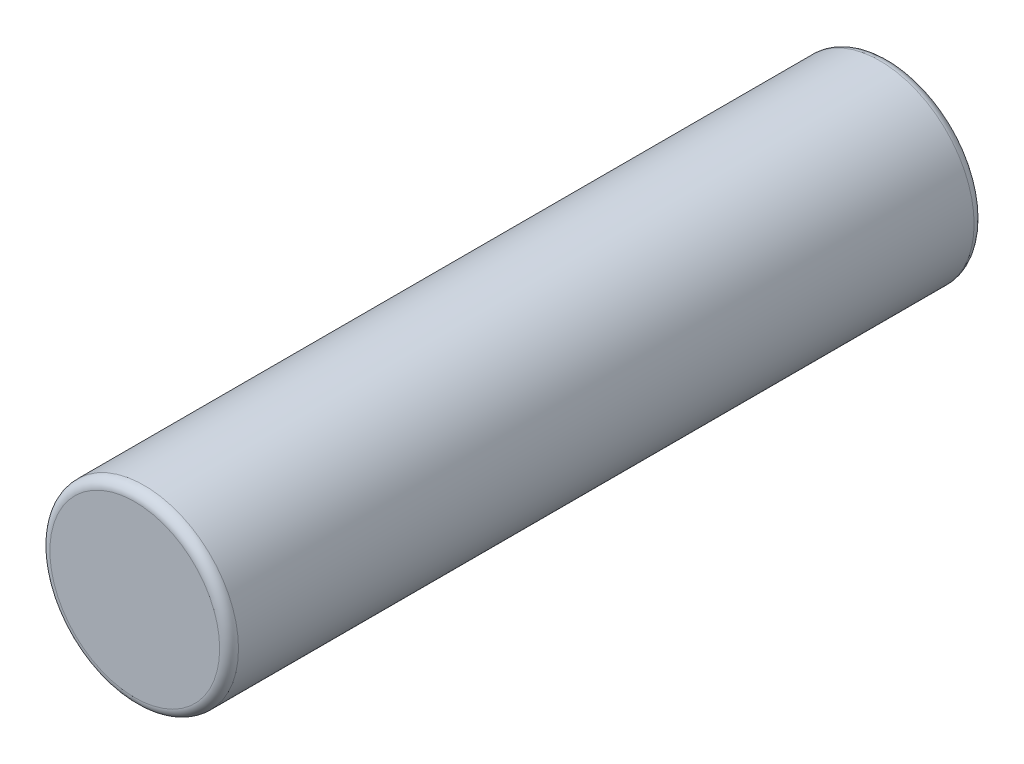
SolidWorks part; units mm, degrees
ref_plane "Front Plane" through (0, 0, 0) normal (0, 0, 1) x (1, 0, 0)
ref_plane "Top Plane" through (0, 0, 0) normal (0, 1, 0) x (1, 0, 0)
ref_plane "Right Plane" through (0, 0, 0) normal (1, 0, 0) x (0, 0, -1)
sketch "Sketch1" plane through (0, 0, 0) normal (0, 0, 1) x (1, 0, 0)
  circle A0 centre (0, 0) radius 20
  dimension "D1" = 40
extrude "Boss-Extrude1" add sketch "Sketch1" along normal blind 160
fillet "Fillet1" radius 2 2 edges at (20, 0, 0) (20, 0, 160)
